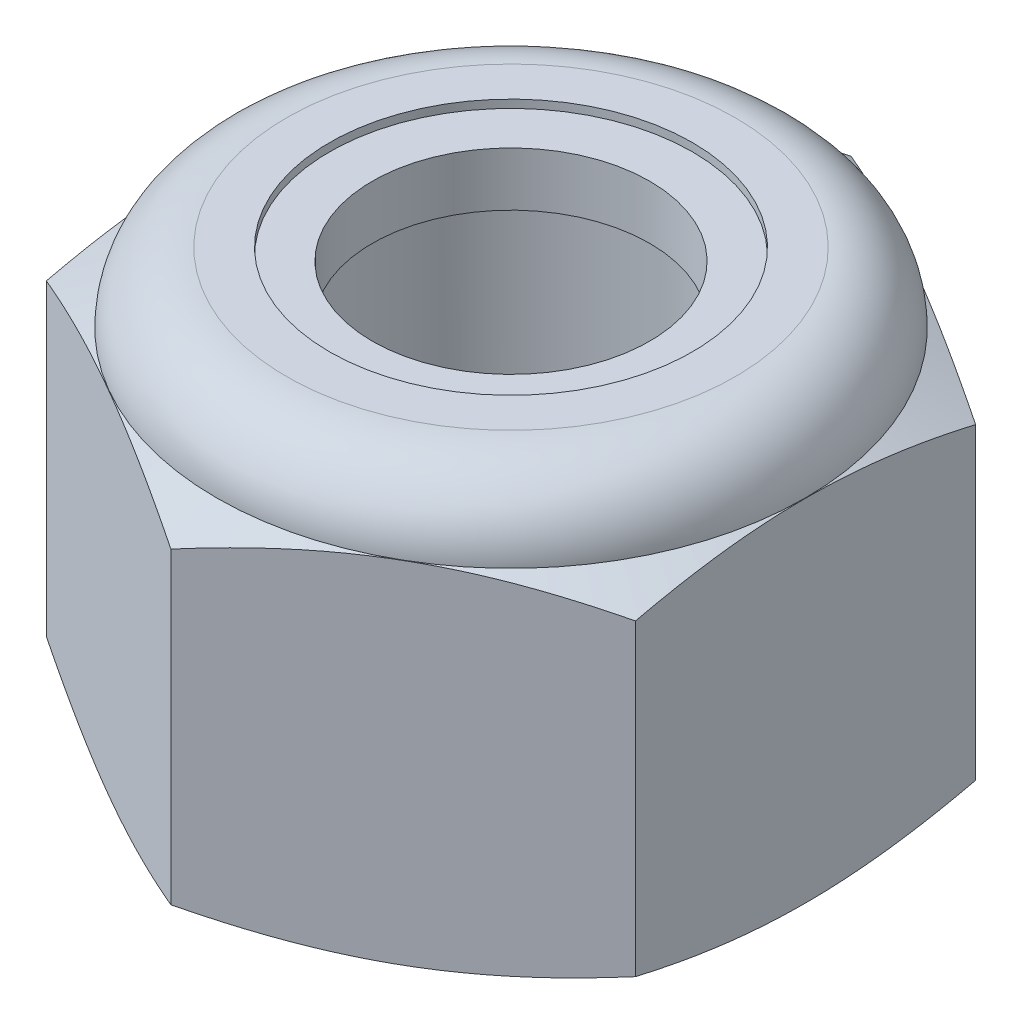
SolidWorks part; units mm, degrees
material "Alloy Steel"
ref_plane "Front Plane" through (0, 0, 0) normal (0, 0, 1) x (1, 0, 0)
ref_plane "Top Plane" through (0, 0, 0) normal (0, 1, 0) x (1, 0, 0)
ref_plane "Right Plane" through (0, 0, 0) normal (1, 0, 0) x (0, 0, -1)
sketch "Sketch1" plane through (0, 0, 0) normal (0, 1, 0) x (1, 0, 0)
  line L0 (0, 0) -> (0, 6.4158) construction
  line L2 (0, 6.4158) -> (-5.5563, 3.2079)
  line L3 (-5.5563, 3.2079) -> (-5.5563, -3.2079)
  line L4 (-5.5563, -3.2079) -> (0, -6.4158)
  line L5 (0, -6.4158) -> (5.5562, -3.2079)
  line L6 (5.5562, -3.2079) -> (5.5562, 3.2079)
  line L7 (5.5562, 3.2079) -> (0, 6.4158)
  circle A0 centre (0, 0) radius 5.5563 construction
  dimension "D1" = 11.1125
extrude "Boss-Extrude1" add sketch "Sketch1" along normal blind 7.9375
sketch "Sketch2" plane through (0, 7.9375, 0) normal (0, 1, 0) x (1, 0, 0)
  circle A0 centre (0, 0) radius 3.175
  dimension "D1" = 6.35
extrude "Cut-Extrude1" cut sketch "Sketch2" against normal through all
sketch "Sketch4" plane through (0, 0, 0) normal (1, 0, 0) x (0, 0, -1)
  line L0 (0, 0) -> (5.5522, 0)
  line L2 (6.4158, 7.9375) -> (6.4158, 0) construction
  line L3 (6.4158, 0.4027) -> (6.4158, 6.214)
  line L4 (6.4158, 6.214) -> (5.5522, 6.6167)
  line L5 (3.2079, 7.9375) -> (6.4158, 7.9375) construction
  line L6 (4.2314, 7.9375) -> (4.2314, 9.2075)
  line L7 (4.2314, 9.2075) -> (7.6858, 9.2075)
  line L8 (7.6858, 9.2075) -> (7.6858, -1.27)
  line L9 (7.6858, -1.27) -> (0, -1.27)
  line L10 (0, -1.27) -> (0, 0)
  line L11 (-3.2079, 0) -> (3.2079, 0) construction
  line L12 (3.2079, 0) -> (6.4158, 0) construction
  line L13 (5.5522, 0) -> (6.4158, 0.4027)
  line L14 (5.5522, 0) -> (5.5522, 6.6167) construction
  line L15 (0, 0) -> (0, 9.6306) construction
  arc A0 (5.5522, 6.6167) -> (4.2314, 7.9375) centre (4.2314, 6.6167) ccw
  dimension "D1" = 1.27
  dimension "D2" = 25
  dimension "D3" = 1.3208
  dimension "D4" = 0.8636
  dimension "D5" = 1.27
revolve "Cut-Revolve1" cut sketch "Sketch4" angle 360 about L15
sketch "Sketch5" plane through (0, 0, 0) normal (1, 0, 0) x (0, 0, -1)
  line L0 (5.3998, 6.6167) -> (0, 6.6167)
  line L1 (5.5522, 6.6167) -> (-5.5522, 6.6167) construction
  line L2 (0, 6.6167) -> (0, 9.1567)
  line L3 (0, 9.1567) -> (3.4216, 9.1567)
  line L4 (3.4216, 9.1567) -> (3.4216, 7.7851)
  line L5 (3.4216, 7.7851) -> (4.2314, 7.7851)
  line L6 (4.2314, 7.7851) -> (4.2314, 7.9375) construction
  line L7 (4.2314, 7.9375) -> (-4.2314, 7.9375) construction
  arc A0 (4.2314, 7.7851) -> (5.3998, 6.6167) centre (4.2314, 6.6167) cw
  arc A1 (5.5522, 6.6167) -> (4.2314, 7.9375) centre (4.2314, 6.6167) ccw construction
  dimension "D1" = 0.1524
  dimension "D2" = 3.4216
  dimension "D3" = 2.54
revolve "Cut-Revolve2" cut sketch "Sketch5" angle 360 about L2
sketch "Sketch6" plane through (0, 0, 0) normal (1, 0, 0) x (0, 0, -1)
  line L1 (2.6162, 6.6929) -> (2.6162, 7.7089)
  line L2 (2.6162, 7.7089) -> (4.2314, 7.7089)
  line L5 (-4.2314, 7.7851) -> (4.2314, 7.7851) construction
  line L6 (5.3209, 6.6929) -> (2.6162, 6.6929)
  line L7 (5.5522, 6.6167) -> (-5.5522, 6.6167) construction
  line L8 (0, 0) -> (0, 7.9375) construction
  line L9 (3.4216, 7.9375) -> (-3.4216, 7.9375) construction
  arc A0 (5.3209, 6.6929) -> (4.2314, 7.7089) centre (4.2314, 6.6167) ccw
  arc A4 (5.3998, 6.6167) -> (4.2314, 7.7851) centre (4.2314, 6.6167) ccw construction
  dimension "D1" = 0.0762
  dimension "D2" = 0.0762
  dimension "D3" = 2.6162
revolve "Revolve1" add sketch "Sketch6" angle 360 about L8
